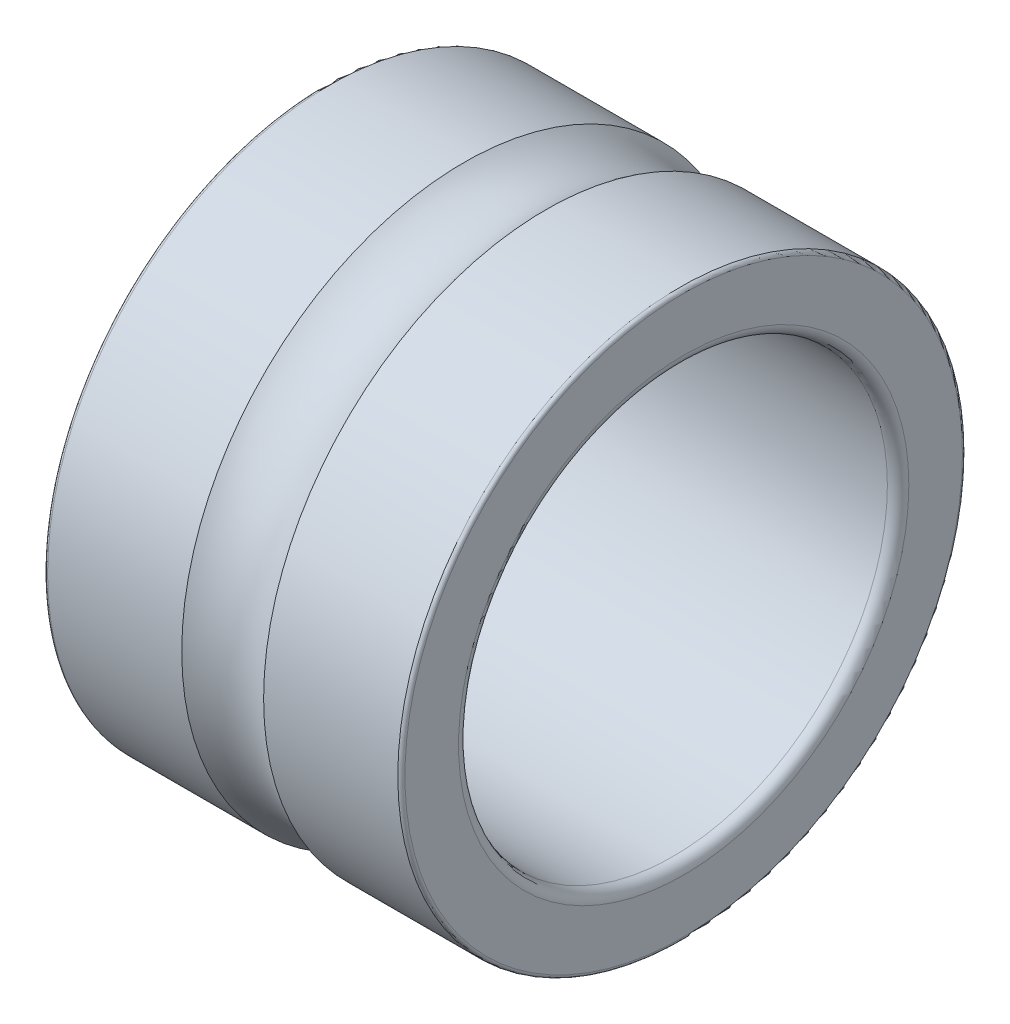
SolidWorks part; units mm, degrees
ref_plane "Front Plane" through (0, 0, 0) normal (0, 0, 1) x (1, 0, 0)
ref_plane "Top Plane" through (0, 0, 0) normal (0, 1, 0) x (1, 0, 0)
ref_plane "Right Plane" through (0, 0, 0) normal (1, 0, 0) x (0, 0, -1)
ref_plane "Plane1" through (0, 0, 0) normal (0, 0, 1) x (1, 0, 0)
sketch "Sketch1" plane through (0, 0, 0) normal (0, 0, 1) x (1, 0, 0)
  line L0 (0, 3.9) -> (0, 3.15)
  line L1 (0.15, 3) -> (4.85, 3)
  line L2 (5, 3.15) -> (5, 3.9)
  line L3 (4.95, 3.95) -> (3.0727, 3.95)
  line L4 (1.9273, 3.95) -> (0.05, 3.95)
  line L5 (4.85, 0) -> (0.15, 0) construction
  arc A0 (0, 3.15) -> (0.15, 3) centre (0.15, 3.15) ccw
  arc A1 (4.85, 3) -> (5, 3.15) centre (4.85, 3.15) ccw
  arc A2 (5, 3.9) -> (4.95, 3.95) centre (4.95, 3.9) ccw
  arc A3 (3.0727, 3.95) -> (1.9273, 3.95) centre (2.5, 4.76) cw
  arc A4 (0.05, 3.95) -> (0, 3.9) centre (0.05, 3.9) ccw
revolve "Revolve1" add sketch "Sketch1" angle 360 about L5
